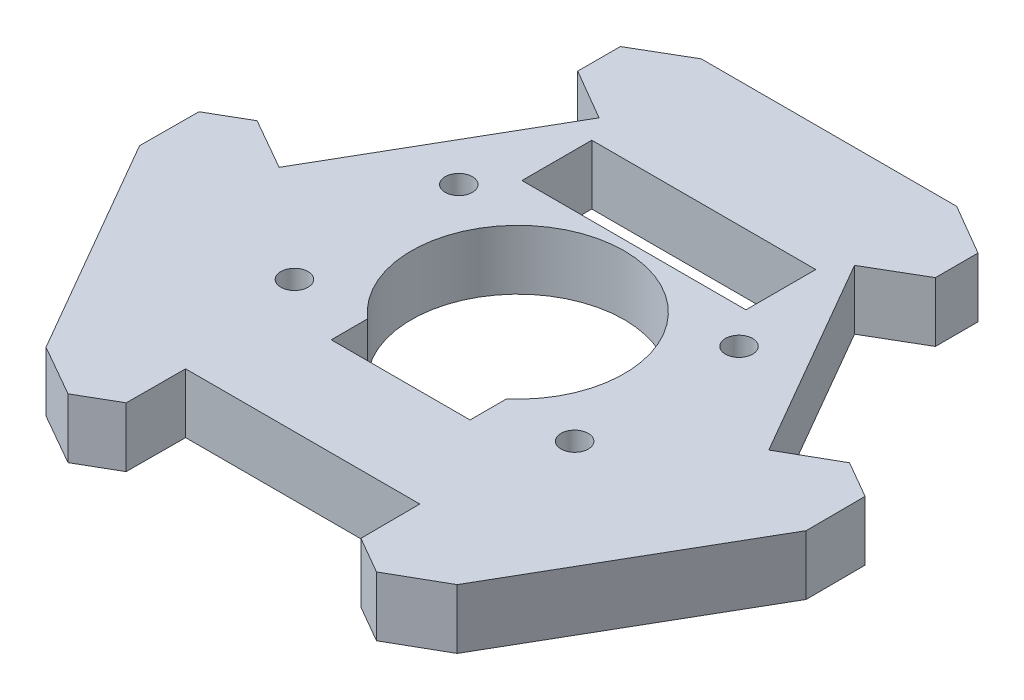
SolidWorks part; units mm, degrees
ref_plane "Front Plane" through (0, 0, 0) normal (0, 0, 1) x (1, 0, 0)
ref_plane "Top Plane" through (0, 0, 0) normal (0, 1, 0) x (1, 0, 0)
ref_plane "Right Plane" through (0, 0, 0) normal (1, 0, 0) x (0, 0, -1)
sketch "Sketch1" plane through (0, 0, 0) normal (0, 1, 0) x (1, 0, 0)
  line L0 (0, 0) -> (85.7802, 0) construction
  line L1 (85.7802, 0) -> (42.8901, 74.2878) construction
  line L2 (42.8901, 74.2878) -> (0, 0) construction
  line L3 (42.8901, 74.2878) -> (42.8901, 24.7626) construction
  line L4 (0, 0) -> (42.8901, 24.7626) construction
  line L5 (85.7802, 0) -> (42.8901, 24.7626) construction
  line L6 (-20.3945, 61.3) -> (106.1747, 61.3) construction
  line L7 (-20.3945, 61.3) -> (42.8901, -48.3122) construction
  line L8 (42.8901, -48.3122) -> (106.1747, 61.3) construction
  line L9 (42.8901, 24.7626) -> (74.5324, 6.4939) construction
  line L10 (42.8901, 24.7626) -> (42.8901, 61.3) construction
  line L11 (42.8901, 24.7626) -> (11.2478, 6.4939) construction
  line L12 (27.8901, 61.3) -> (57.8901, 61.3)
  line L13 (57.8901, 61.3) -> (63.8901, 57.8)
  line L14 (63.8901, 57.8) -> (63.8901, 52.8)
  line L15 (63.8901, 52.8) -> (57.8901, 49.3)
  line L16 (57.8901, 49.3) -> (64.7651, 37.3922)
  line L17 (64.3352, 37.1439) -> (64.7651, 37.3922) construction
  line L18 (27.8901, 61.3) -> (21.8901, 57.8)
  line L19 (21.8901, 57.8) -> (21.8901, 52.8)
  line L20 (21.8901, 52.8) -> (27.8901, 49.3)
  line L21 (27.8901, 49.3) -> (21.0151, 37.3922)
  line L22 (56.6401, -0.4965) -> (42.8901, -0.4965)
  line L23 (56.6712, -7.4426) -> (56.6401, -0.4965)
  line L24 (61.0013, -9.9426) -> (56.6712, -7.4426)
  line L25 (67.0324, -6.4965) -> (61.0013, -9.9426)
  line L26 (82.0324, 19.4843) -> (67.0324, -6.4965)
  line L27 (82.0324, 19.4843) -> (82.0013, 26.4305)
  line L28 (82.0013, 26.4305) -> (77.6712, 28.9305)
  line L29 (77.6712, 28.9305) -> (71.6401, 25.4843)
  line L30 (71.6401, 25.4843) -> (64.7651, 37.3922)
  line L31 (14.1401, 25.4843) -> (21.0151, 37.3922)
  line L32 (8.109, 28.9305) -> (14.1401, 25.4843)
  line L33 (3.7789, 26.4305) -> (8.109, 28.9305)
  line L34 (3.7478, 19.4843) -> (3.7789, 26.4305)
  line L35 (18.7478, -6.4965) -> (3.7478, 19.4843)
  line L36 (18.7478, -6.4965) -> (24.7789, -9.9426)
  line L37 (24.7789, -9.9426) -> (29.109, -7.4426)
  line L38 (29.109, -7.4426) -> (29.1401, -0.4965)
  line L39 (29.1401, -0.4965) -> (42.8901, -0.4965)
  point P4 (0, 0)
  point P16 (21.0151, 37.3922)
  point P45 (42.8901, 24.7626)
  dimension "D1" = 61.3
  dimension "D2" = 30
  dimension "D3" = 5
  dimension "D4" = 90
  dimension "D5" = 6
  dimension "D6" = 12
  dimension "D8" = 27.5
  dimension "D7" = 3
extrude "Boss-Extrude3" add sketch "Sketch1" along normal blind 7 contours L38 L39 L22 L23 L24 L25 L26 L27 L28 L29 L30 L16 L15 L14 L13 L12 L18 L19 L20 L21 L31 L32 L33 L34 L35 L36 L37
sketch "Sketch2" plane through (0, 7, 0) normal (0, 1, 0) x (1, 0, 0)
  line L0 (42.8901, 61.3) -> (42.8901, 24.7626) construction
  line L1 (27.8901, 61.3) -> (57.8901, 61.3) construction
  line L2 (11.2478, 6.4939) -> (42.8901, 24.7626) construction
  line L3 (18.7478, -6.4965) -> (3.7478, 19.4843) construction
  line L4 (74.5324, 6.4939) -> (42.8901, 24.7626) construction
  line L5 (82.0324, 19.4843) -> (67.0324, -6.4965) construction
  line L6 (34.7401, 11.0035) -> (51.0401, 11.0035)
  line L7 (42.8901, -0.4965) -> (42.8901, 11.0035) construction
  line L8 (29.1401, -0.4965) -> (56.6401, -0.4965) construction
  line L9 (34.7401, 11.0035) -> (34.7401, 15.2849)
  line L10 (51.0401, 11.0035) -> (51.0401, 15.2849)
  line L11 (59.3425, 34.2843) -> (59.3425, 14.9843) construction
  line L12 (71.6401, 25.4843) -> (57.8901, 49.3) construction
  line L14 (29.7401, 46.6) -> (56.0401, 46.6)
  line L15 (29.7401, 46.6) -> (29.7401, 38.4)
  line L16 (29.7401, 38.4) -> (56.0401, 38.4)
  line L17 (56.0401, 46.6) -> (56.0401, 38.4)
  line L18 (29.7401, 46.6) -> (56.0401, 38.4) construction
  line L19 (29.7401, 38.4) -> (56.0401, 46.6) construction
  arc A0 (51.0401, 15.2849) -> (34.7401, 15.2849) centre (42.8901, 24.7626) ccw
  circle A1 centre (59.3425, 34.2843) radius 1.6
  circle A2 centre (59.3425, 14.9843) radius 1.6
  circle A3 centre (26.4377, 14.9843) radius 1.6
  circle A4 centre (26.4377, 34.2843) radius 1.6
  point P29 (42.8901, 42.5)
  dimension "D1" = 25
  dimension "D4" = 3.2
  dimension "D6" = 16.1
  dimension "D2" = 16.3
  dimension "D3" = 11.5
  dimension "D5" = 4.65
  dimension "D7" = 15.8
  dimension "D8" = 8.2
  dimension "D9" = 26.3
  dimension "D10" = 14.7
extrude "Cut-Extrude1" cut sketch "Sketch2" against normal through all
